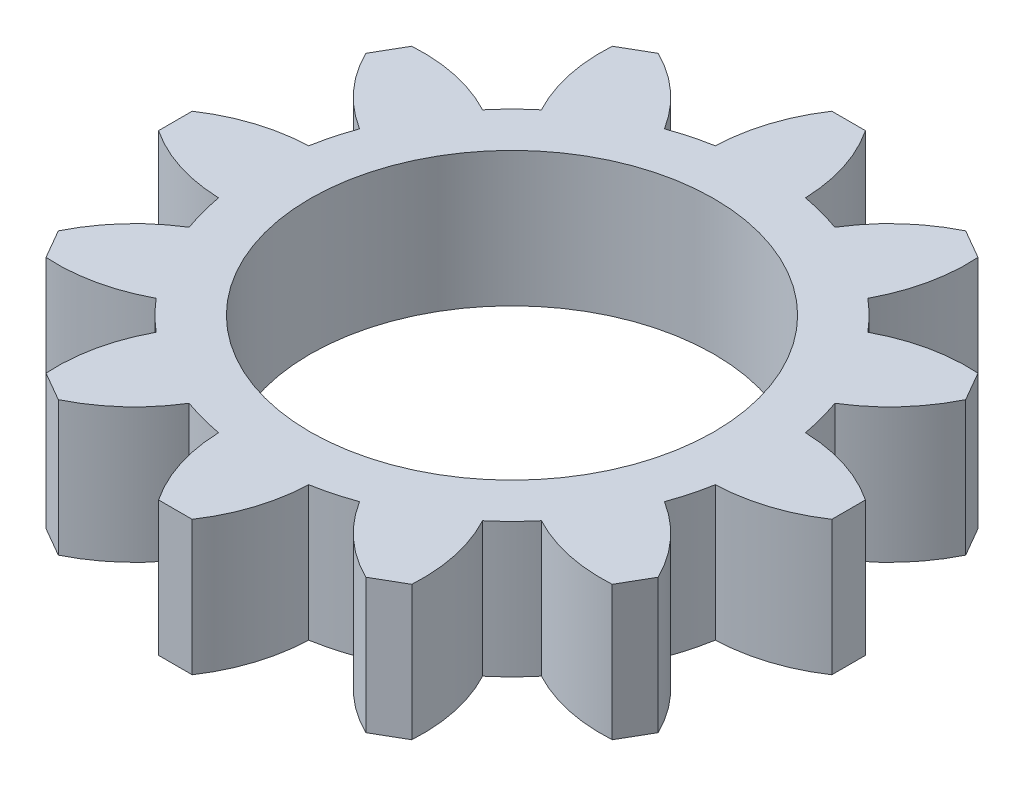
SolidWorks part; units mm, degrees
ref_plane "Front Plane" through (0, 0, 0) normal (0, 0, 1) x (1, 0, 0)
ref_plane "Top Plane" through (0, 0, 0) normal (0, 1, 0) x (1, 0, 0)
ref_plane "Right Plane" through (0, 0, 0) normal (1, 0, 0) x (0, 0, -1)
sketch "Sketch1" plane through (0, 0, 0) normal (0, 1, 0) x (1, 0, 0)
  line L0 (0, 0) -> (0, 25.6471) construction
  line L1 (-1, 20) -> (1, 20)
  line L2 (9.134, 17.8205) -> (10.866, 16.8205)
  line L3 (16.8205, 10.866) -> (17.8205, 9.134)
  line L4 (20, 1) -> (20, -1)
  line L5 (17.8205, -9.134) -> (16.8205, -10.866)
  line L6 (10.866, -16.8205) -> (9.134, -17.8205)
  line L7 (1, -20) -> (-1, -20)
  line L8 (-9.134, -17.8205) -> (-10.866, -16.8205)
  line L9 (-16.8205, -10.866) -> (-17.8205, -9.134)
  line L10 (-20, -1) -> (-20, 1)
  line L11 (-17.8205, 9.134) -> (-16.8205, 10.866)
  line L12 (-10.866, 16.8205) -> (-9.134, 17.8205)
  circle A0 centre (0, 0) radius 12
  arc A1 (-2.675, 14.7596) -> (-5.0632, 14.1196) centre (0, 0) ccw
  arc A2 (-1, 20) -> (-2.675, 14.7596) centre (7.3203, 14.4527) ccw
  arc A3 (1, 20) -> (2.675, 14.7596) centre (-7.3203, 14.4527) cw
  arc A4 (9.134, 17.8205) -> (5.0632, 14.1196) centre (13.5659, 8.8562) ccw
  arc A5 (10.866, 16.8205) -> (9.6964, 11.4446) centre (0.8868, 16.1765) cw
  arc A6 (16.8205, 10.866) -> (11.4446, 9.6964) centre (16.1765, 0.8868) ccw
  arc A7 (17.8205, 9.134) -> (14.1196, 5.0632) centre (8.8562, 13.5659) cw
  arc A8 (20, 1) -> (14.7596, 2.675) centre (14.4527, -7.3203) ccw
  arc A9 (20, -1) -> (14.7596, -2.675) centre (14.4527, 7.3203) cw
  arc A10 (17.8205, -9.134) -> (14.1196, -5.0632) centre (8.8562, -13.5659) ccw
  arc A11 (16.8205, -10.866) -> (11.4446, -9.6964) centre (16.1765, -0.8868) cw
  arc A12 (10.866, -16.8205) -> (9.6964, -11.4446) centre (0.8868, -16.1765) ccw
  arc A13 (9.134, -17.8205) -> (5.0632, -14.1196) centre (13.5659, -8.8562) cw
  arc A14 (1, -20) -> (2.675, -14.7596) centre (-7.3203, -14.4527) ccw
  arc A15 (-1, -20) -> (-2.675, -14.7596) centre (7.3203, -14.4527) cw
  arc A16 (-9.134, -17.8205) -> (-5.0632, -14.1196) centre (-13.5659, -8.8562) ccw
  arc A17 (-10.866, -16.8205) -> (-9.6964, -11.4446) centre (-0.8868, -16.1765) cw
  arc A18 (-16.8205, -10.866) -> (-11.4446, -9.6964) centre (-16.1765, -0.8868) ccw
  arc A19 (-17.8205, -9.134) -> (-14.1196, -5.0632) centre (-8.8562, -13.5659) cw
  arc A20 (-20, -1) -> (-14.7596, -2.675) centre (-14.4527, 7.3203) ccw
  arc A21 (-20, 1) -> (-14.7596, 2.675) centre (-14.4527, -7.3203) cw
  arc A22 (-17.8205, 9.134) -> (-14.1196, 5.0632) centre (-8.8562, 13.5659) ccw
  arc A23 (-16.8205, 10.866) -> (-11.4446, 9.6964) centre (-16.1765, 0.8868) cw
  arc A24 (-10.866, 16.8205) -> (-9.6964, 11.4446) centre (-0.8868, 16.1765) ccw
  arc A25 (-9.134, 17.8205) -> (-5.0632, 14.1196) centre (-13.5659, 8.8562) cw
  arc A26 (-9.6964, 11.4446) -> (-11.4446, 9.6964) centre (0, 0) ccw
  arc A27 (5.0632, 14.1196) -> (2.675, 14.7596) centre (0, 0) ccw
  arc A28 (11.4446, 9.6964) -> (9.6964, 11.4446) centre (0, 0) ccw
  arc A29 (14.7596, 2.675) -> (14.1196, 5.0632) centre (0, 0) ccw
  arc A30 (14.1196, -5.0632) -> (14.7596, -2.675) centre (0, 0) ccw
  arc A31 (9.6964, -11.4446) -> (11.4446, -9.6964) centre (0, 0) ccw
  arc A32 (2.675, -14.7596) -> (5.0632, -14.1196) centre (0, 0) ccw
  arc A33 (-5.0632, -14.1196) -> (-2.675, -14.7596) centre (0, 0) ccw
  arc A34 (-11.4446, -9.6964) -> (-9.6964, -11.4446) centre (0, 0) ccw
  arc A35 (-14.7596, -2.675) -> (-14.1196, -5.0632) centre (0, 0) ccw
  arc A36 (-14.1196, 5.0632) -> (-14.7596, 2.675) centre (0, 0) ccw
  point P9 (0, 20)
  point P81 (0, 0)
  dimension "D1" = 30
  dimension "D2" = 24
  dimension "D5" = 10
  dimension "D3" = 2
  dimension "D4" = 20
  dimension "D6" = 5.35
  dimension "D7" = 12
extrude "Boss-Extrude1" add sketch "Sketch1" along normal mid plane 8
